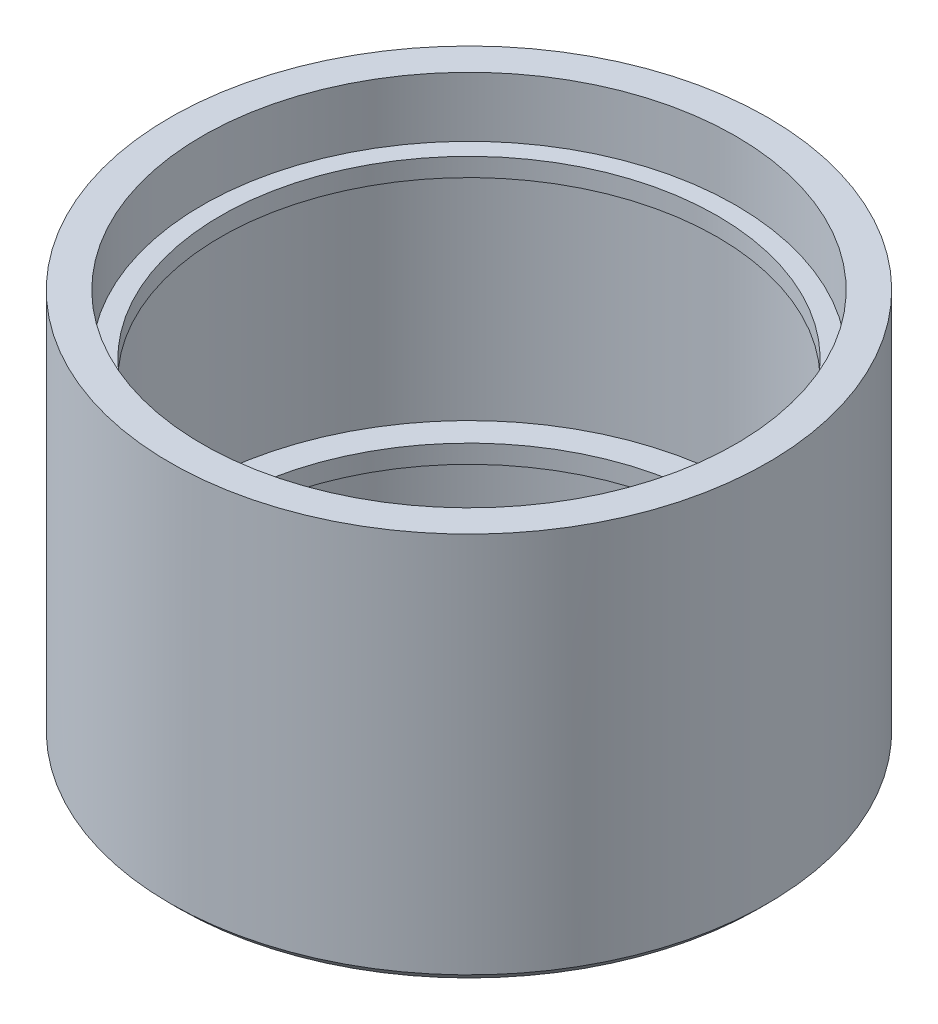
SolidWorks part; units mm, degrees
material "Ductile Iron"
ref_plane "Front Plane" through (0, 0, 0) normal (0, 0, 1) x (1, 0, 0)
ref_plane "Top Plane" through (0, 0, 0) normal (0, 1, 0) x (1, 0, 0)
ref_plane "Right Plane" through (0, 0, 0) normal (1, 0, 0) x (0, 0, -1)
sketch "Sketch3" plane through (0, 0, 0) normal (1, 0, 0) x (0, 0, -1)
  line L0 (0, -21.25) -> (0, 21.25) construction
  line L1 (-29, -21.25) -> (-29, -14.25)
  line L2 (-29, -14.25) -> (-27, -14.25)
  line L3 (-27, -14.25) -> (-27, -12.25)
  line L4 (-30, -12.25) -> (-27, -12.25)
  line L5 (-40.7081, 0) -> (40.7081, 0) construction
  line L10 (-29, -21.25) -> (-32.5, -21.25)
  line L11 (-32.5, -21.25) -> (-32.5, 21.25)
  line L12 (-32.5, 21.25) -> (-29, 21.25)
  line L19 (-29, 21.25) -> (-29, 14.75)
  line L20 (-29, 14.75) -> (-27, 14.75)
  line L21 (-27, 14.75) -> (-27, 12.75)
  line L22 (-27, 12.75) -> (-30, 12.75)
  line L23 (-30, 12.75) -> (-30, -12.25)
  point P10 (0, 0)
  dimension "D1" = 7
  dimension "D2" = 2
  dimension "D3" = 2
  dimension "D4" = 58
  dimension "D5" = 65
  dimension "D6" = 42.5
  dimension "D7" = 6.5
  dimension "D8" = 60
revolve "Revolve2" add sketch "Sketch3" angle 360 about L0
chamfer "Chamfer1" distance 1 angle 45 1 edges at (0, -21.25, -32.5)
